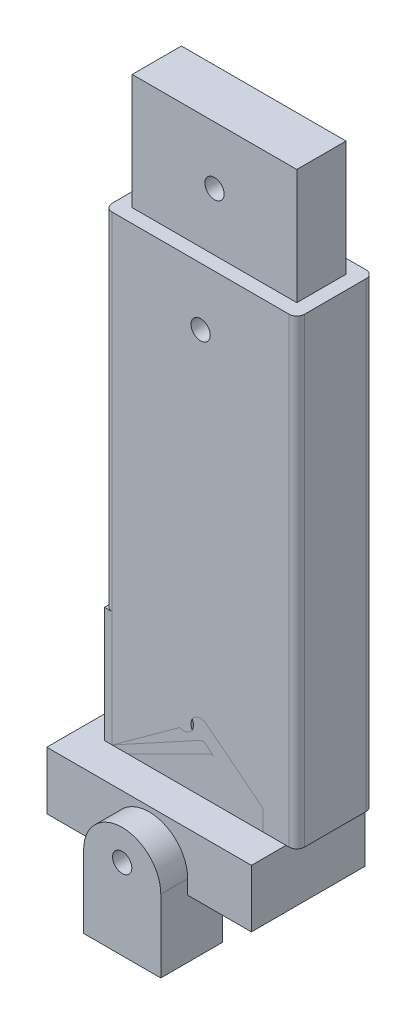
SolidWorks part; units mm, degrees
ref_plane "Front Plane" through (0, 0, 0) normal (0, 0, 1) x (1, 0, 0)
ref_plane "Top Plane" through (0, 0, 0) normal (0, 1, 0) x (1, 0, 0)
ref_plane "Right Plane" through (0, 0, 0) normal (1, 0, 0) x (0, 0, -1)
sketch "Sketch1" plane through (0, 0, 0) normal (0, 1, 0) x (1, 0, 0)
  line L1 (2, 0) -> (48, 0)
  line L2 (0, 2) -> (0, 18)
  line L3 (2, 20) -> (48, 20)
  line L4 (50, 2) -> (50, 18)
  arc A0 (2, 0) -> (0, 2) centre (2, 2) cw
  arc A1 (48, 0) -> (50, 2) centre (48, 2) ccw
  arc A2 (48, 20) -> (50, 18) centre (48, 18) cw
  arc A3 (0, 18) -> (2, 20) centre (2, 18) cw
  point P7 (0, 0)
  point P12 (50, 20)
  point P15 (0, 20)
  dimension "D3" = 2
  dimension "D1" = 50
  dimension "D2" = 20
extrude "Boss-Extrude1" add sketch "Sketch1" along normal blind 120
sketch "Sketch3" plane through (0, 0, 0) normal (0, -1, 0) x (1, 0, 0)
  line L29 (46, -16) -> (46, -4)
  line L30 (4, -16) -> (46, -16)
  line L31 (4, -4) -> (4, -16)
  line L32 (46, -4) -> (4, -4)
  line L33 (46, -16) -> (46, -4)
  line L34 (4, -16) -> (46, -16)
  line L35 (4, -4) -> (4, -16)
  line L36 (46, -4) -> (4, -4)
  dimension "D1" = 4
extrude "Cut-Extrude2" cut sketch "Sketch3" against normal blind 30 contours L35 L34 L33 L36
sketch "Sketch6" plane through (0, 0, 0) normal (0, 0, 1) x (1, 0, 0)
  line L0 (50, 120) -> (50, 0) construction
  line L1 (2, 120) -> (48, 120) construction
  line L2 (2, 0) -> (48, 0) construction
  circle A0 centre (25, 105) radius 2.5
  circle A1 centre (25, 15) radius 2.5
  dimension "D1" = 25
  dimension "D3" = 15
  dimension "D2" = 15
extrude "Cut-Extrude3" cut sketch "Sketch6" against normal blind 30
sketch "Sketch8" plane through (0, 120, 0) normal (0, 1, 0) x (1, 0, 0)
  line L20 (3.6, 16.4) -> (3.6, 3.6)
  line L21 (3.6, 3.6) -> (46.4, 3.6)
  line L22 (46.4, 3.6) -> (46.4, 16.4)
  line L23 (46.4, 16.4) -> (3.6, 16.4)
  line L24 (3.6, 16.4) -> (3.6, 3.6)
  line L25 (3.6, 3.6) -> (46.4, 3.6)
  line L26 (46.4, 3.6) -> (46.4, 16.4)
  line L27 (46.4, 16.4) -> (3.6, 16.4)
  dimension "D1" = 3.6
extrude "Boss-Extrude2" add sketch "Sketch8" along normal blind 30
sketch "Sketch9" plane through (0, 0, -3.6) normal (0, 0, 1) x (1, 0, 0)
  line L0 (46.4, 150) -> (46.4, 120) construction
  line L1 (3.6, 150) -> (46.4, 150) construction
  circle A0 centre (25, 135) radius 2.5
  dimension "D1" = 21.4
  dimension "D2" = 15
extrude "Cut-Extrude4" cut sketch "Sketch9" against normal blind 30
sketch "Sketch11" plane through (0, 0, 0) normal (0, 1, 0) x (1, 0, 0)
  line L1 (0, 0) -> (41.2, 0)
  line L2 (0, 0) -> (0, 11.5)
  line L3 (0, 11.5) -> (41.2, 11.5)
  line L4 (41.2, 0) -> (41.2, 11.5)
  dimension "D1" = 41.2
  dimension "D2" = 11.5
extrude "Boss-Extrude3" add sketch "Sketch11" along normal blind 30 separate body
hole_wizard "Ø5.0 (5) Diameter Hole1" positions "Sketch12" profile "Sketch13" hole size "Ø5.0" standard "ANSI Metric" end condition through all
sketch "Sketch12" plane through (0, 0, 0) normal (0, 0, 1) x (1, 0, 0)
  line L0 (0, 30) -> (41.2, 30) construction
  line L1 (41.2, 30) -> (41.2, 0) construction
  point P0 (20.6, 15)
  dimension "D1" = 15
  dimension "D2" = 20.6
sketch "Sketch13" plane through (20.6, 15, 0) normal (1, 0, 0) x (0, -1, 0)
  line L0 (0, 0) -> (0, 20)
  line L1 (0, 20) -> (2.5, 20)
  line L2 (2.5, 20) -> (2.5, 0.021)
  line L3 (2.5, 0.021) -> (2.525, 0)
  line L5 (2.525, 0) -> (0, 0)
  line L6 (-2.5, 0.021) -> (-2.525, 0) construction
  line L11 (0, -6.35) -> (0, 107.95) construction
  dimension "Thru Hole Dia." = 5
  dimension "Thru Hole Depth" = 20
  dimension "Near C'Sink Dia." = 5.05
  dimension "Near C'Sink Angle" = 100
sketch "Sketch15" plane through (0, 0, 0) normal (0, 0, 1) x (1, 0, 0)
  line L0 (0, 0) -> (0, -15.1097)
  line L1 (41.2, 0) -> (41.2, -15.1097)
  line L2 (0, 0) -> (41.2, 0)
  arc A0 (0, -15.1097) -> (41.2, -15.1097) centre (20.6, -23.3449) cw
extrude "Boss-Extrude4" add sketch "Sketch15" against normal blind 14.5 and the other way blind 3 contours L0 A0 L1 L2
sketch "Sketch16" plane through (0, 0, 0) normal (0, 1, 0) x (1, 0, 0)
  line L37 (0, 14.5) -> (41.2, 14.5)
  line L38 (0, 14.5) -> (0, -3)
  line L39 (0, -3) -> (41.2, -3)
  line L40 (41.2, 14.5) -> (41.2, -3)
  line L44 (-6, 20.5) -> (-6, 11.5)
  line L45 (-6, 11.5) -> (-6, 0)
  line L46 (-6, 0) -> (-6, -9)
  line L47 (-6, -9) -> (47.2, -9)
  line L48 (47.2, -9) -> (47.2, 0)
  line L49 (47.2, 0) -> (47.2, 11.5)
  line L50 (47.2, 11.5) -> (47.2, 20.5)
  line L51 (47.2, 20.5) -> (-6, 20.5)
  line L52 (-6, 20.5) -> (-6, 11.5)
  line L53 (-6, 11.5) -> (-6, 0)
  line L54 (-6, 0) -> (-6, -9)
  line L55 (-6, -9) -> (47.2, -9)
  line L56 (47.2, -9) -> (47.2, 0)
  line L57 (47.2, 0) -> (47.2, 11.5)
  line L58 (47.2, 11.5) -> (47.2, 20.5)
  line L59 (47.2, 20.5) -> (-6, 20.5)
  dimension "D1" = 6
extrude "Boss-Extrude5" add sketch "Sketch16" against normal blind 15
hole_wizard "Ø5.0 (5) Diameter Hole2" positions "Sketch17" profile "Sketch18" hole size "Ø5.0" standard "ANSI Metric" end condition through all
sketch "Sketch17" plane through (0, 0, -20.5) normal (0, 0, -1) x (-1, 0, 0)
  line L0 (6, -15) -> (6, 0) construction
  point P0 (-20.6, -9.147)
  dimension "D1" = 26.6
sketch "Sketch18" plane through (20.6, -9.147, -20.5) normal (1, 0, 0) x (0, 1, 0)
  line L0 (0, 0) -> (0, 29.5)
  line L1 (0, 29.5) -> (2.5, 29.5)
  line L2 (2.5, 29.5) -> (2.5, 0.021)
  line L3 (2.5, 0.021) -> (2.525, 0)
  line L5 (2.525, 0) -> (0, 0)
  line L6 (-2.5, 0.021) -> (-2.525, 0) construction
  line L11 (0, -6.35) -> (0, 107.95) construction
  dimension "Thru Hole Dia." = 5
  dimension "Thru Hole Depth" = 29.5
  dimension "Near C'Sink Dia." = 5.05
  dimension "Near C'Sink Angle" = 100
sketch "Sketch22" plane through (0, 0, 9) normal (0, 0, 1) x (1, 0, 0)
  line L1 (24.0138, -11.0268) -> (23.9348, -7.1305)
  line L2 (23.9348, -7.1305) -> (20.521, -5.2507)
  line L3 (20.521, -5.2507) -> (17.1862, -7.2673)
  line L4 (17.1862, -7.2673) -> (17.2652, -11.1636)
  line L5 (17.2652, -11.1636) -> (20.679, -13.0433)
  line L6 (20.679, -13.0433) -> (24.0138, -11.0268)
  circle A0 centre (20.6, -9.147) radius 3.375 construction
  dimension "D1" = 6.75
extrude "Cut-Extrude5" cut sketch "Sketch22" against normal blind 3.12
sketch "Sketch23" plane through (0, 0, 0) normal (0, 0, 1) x (1, 0, 0)
  line L0 (0, 0) -> (0, -15.1097)
  line L1 (41.2, 0) -> (41.2, -15.1097)
  line L2 (0, 0) -> (41.2, 0)
  arc A0 (0, -15.1097) -> (41.2, -15.1097) centre (20.6, -23.3449) cw
sketch "Sketch24" plane through (0, 0, 0) normal (0, 0, 1) x (1, 0, 0)
  line L0 (10.5738, -11.2823) -> (10.5738, -30.159)
  line L1 (10.5738, -30.159) -> (30.6313, -30.159)
  line L2 (30.6313, -30.159) -> (30.6313, -11.2823)
  arc A0 (10.5738, -11.2823) -> (30.6313, -11.2823) centre (20.6025, -11.2823) cw
  point P0 (20.6025, -11.2823)
extrude "Boss-Extrude6" add sketch "Sketch24" along normal blind 16 separate body
sketch "Sketch25" plane through (0, -30.159, 0) normal (0, -1, 0) x (1, 0, 0)
  line L0 (0, 0) -> (41.2, 0) construction
  circle A0 centre (20.6025, 8) radius 6.975
  point P2 (20.6, 0)
  point P3 (0, 0)
  dimension "D1" = 13.95
  dimension "D2" = 8
extrude "Cut-Extrude6" cut sketch "Sketch25" against normal blind 12
sketch "Sketch29" plane through (0, 0, 0) normal (0, 0, -1) x (-1, 0, 0)
  circle A0 centre (-20.6, -9.147) radius 2.5
extrude "Cut-Extrude8" cut sketch "Sketch29" against normal through all contours A0
